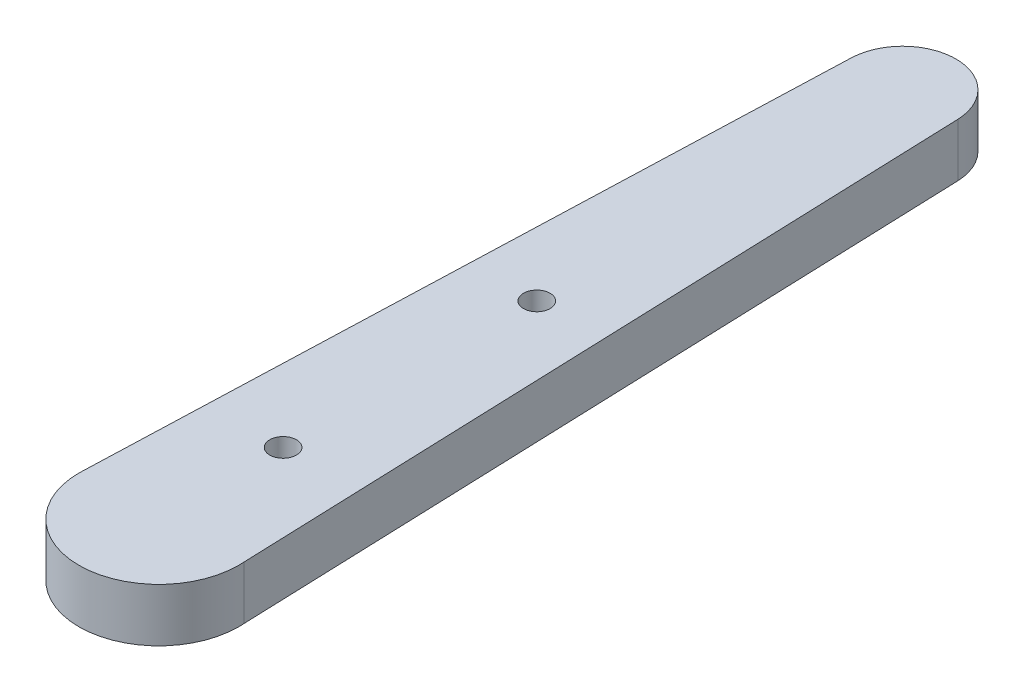
SolidWorks part; units mm, degrees
material "ABS PC"
ref_plane "Front Plane" through (0, 0, 0) normal (0, 0, 1) x (1, 0, 0)
ref_plane "Top Plane" through (0, 0, 0) normal (0, 1, 0) x (1, 0, 0)
ref_plane "Right Plane" through (0, 0, 0) normal (1, 0, 0) x (0, 0, -1)
sketch "Sketch1" plane through (0, 0, 0) normal (0, 1, 0) x (1, 0, 0)
  circle A1 centre (0, 0) radius 3
  dimension "D2" = 6
extrude "Boss-Extrude1" add sketch "Sketch1" along normal blind 2
sketch "Sketch3" plane through (0, 2, 0) normal (0, 1, 0) x (1, 0, 0)
  line L2 (-3, 0) -> (-1.9991, 27.9955)
  line L4 (3, 0) -> (1.9983, 27.9956)
  circle A0 centre (0, 0) radius 3 construction
  arc A1 (-1.9991, 27.9955) -> (1.9983, 27.9956) centre (-0.0004, 27.9241) cw
  arc A5 (-2.9923, 0.2142) -> (2.9923, 0.2144) centre (0, 0) ccw
  point P0 (0, 0)
  point P8 (0, 27.9956)
  point P11 (0, 27.9956)
  point P15 (-3, 0.2144)
  point P16 (-3, 0)
  point P17 (-2.9923, 0)
  point P18 (-3, 0)
  circle M6 centre (0, 0) radius 3
  dimension "D2" = 27.9955
  dimension "D4" = 4.097
  dimension "D1" = 2
  dimension "D3" = 6
  dimension "D6" = 27.9956
extrude "Boss-Extrude4" add sketch "Sketch3" against normal blind 2 contours L4 L2 M6 | A1 L2 L4 M6
sketch "Sketch4" plane through (0, 2, 0) normal (0, 1, 0) x (1, 0, 0)
  line L0 (0, 0) -> (-0.0004, 29.9241) construction
  arc A0 (1.9983, 27.9956) -> (-1.9991, 27.9955) centre (-0.0004, 27.9241) ccw construction
  circle A7 centre (-0.0002, 14.1901) radius 0.5
  circle A8 centre (-0.0001, 4.6651) radius 0.5
  point P7 (0, 0)
  point P9 (0, 0)
  point P12 (-3.6911, 13.4459)
  point P13 (0, 0)
  dimension "D1" = 1
  dimension "D2" = 1
  dimension "D3" = 9.525
  dimension "D4" = 4.6651
extrude "Cut-Extrude1" cut sketch "Sketch4" against normal blind 2
